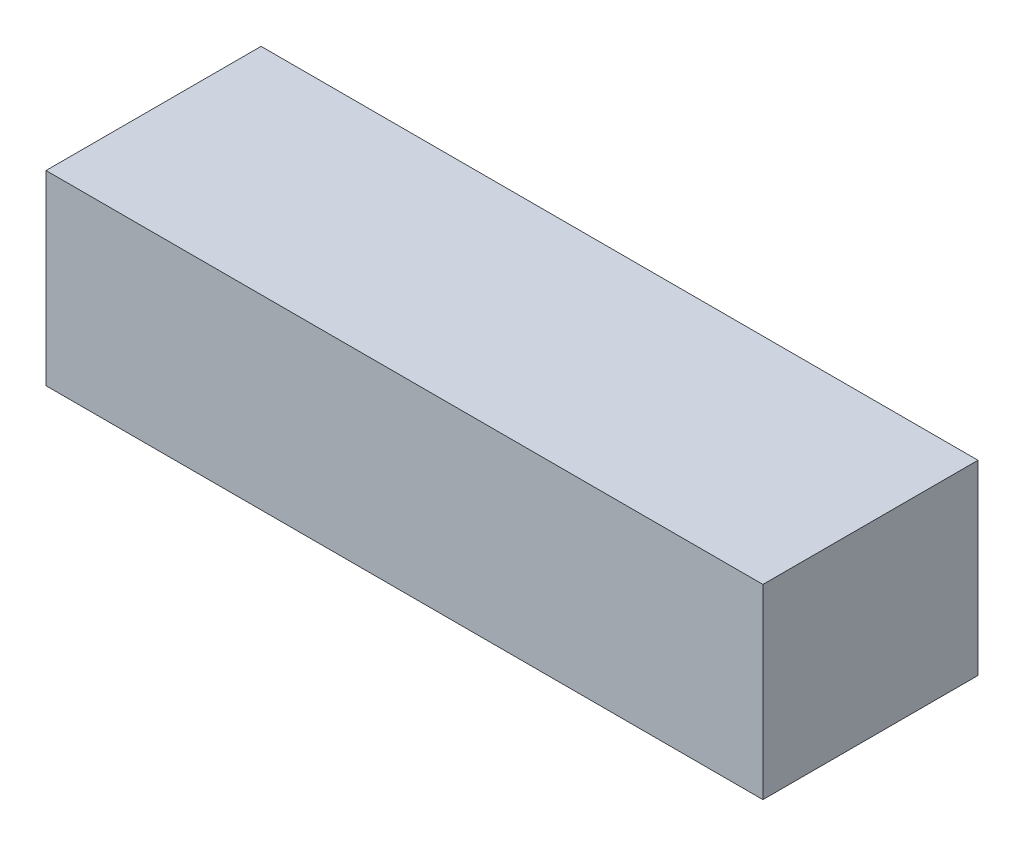
SolidWorks part; units mm, degrees
material "A286 Iron Base Superalloy"
ref_plane "Front Plane" through (0, 0, 0) normal (0, 0, 1) x (1, 0, 0)
ref_plane "Top Plane" through (0, 0, 0) normal (0, 1, 0) x (1, 0, 0)
ref_plane "Right Plane" through (0, 0, 0) normal (1, 0, 0) x (0, 0, -1)
sketch "Sketch1" plane through (0, 0, 0) normal (0, 1, 0) x (1, 0, 0)
  line L1 (250, -75) -> (-250, -75)
  line L2 (250, -75) -> (250, 75)
  line L3 (250, 75) -> (-250, 75)
  line L4 (-250, -75) -> (-250, 75)
  line L5 (250, -75) -> (-250, 75) construction
  line L6 (250, 75) -> (-250, -75) construction
  point P0 (0, 0)
  dimension "D1" = 500
  dimension "D2" = 150
extrude "Boss-Extrude1" add sketch "Sketch1" along normal blind 130
